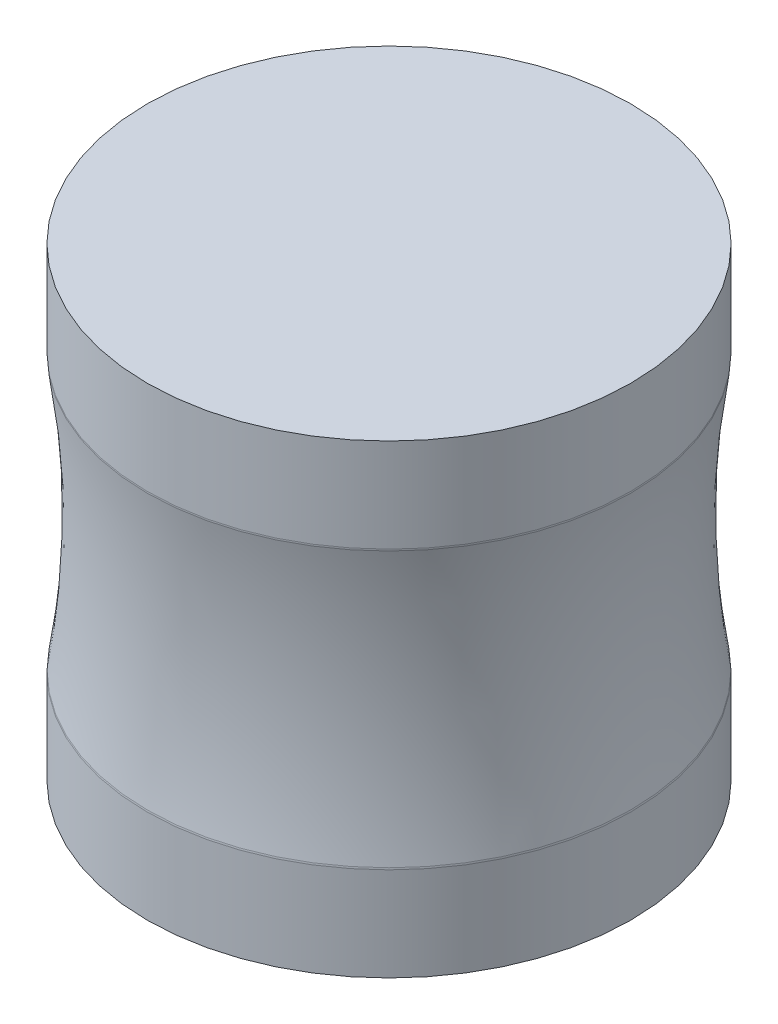
SolidWorks part; units mm, degrees
ref_plane "Ebene vorne" through (0, 0, 0) normal (0, 0, 1) x (1, 0, 0)
ref_plane "Ebene oben" through (0, 0, 0) normal (0, 1, 0) x (1, 0, 0)
ref_plane "Ebene rechts" through (0, 0, 0) normal (1, 0, 0) x (0, 0, -1)
sketch "Skizze1" plane through (0, 0, 0) normal (0, 0, 1) x (1, 0, 0)
  line L0 (109.5273, -62.8727) -> (109.5273, -105.2597)
  line L1 (0, 105.2597) -> (109.5273, 105.2597)
  line L2 (0, 105.2597) -> (0, -105.2597)
  line L3 (0, -105.2597) -> (109.5273, -105.2597)
  line L4 (109.5273, 105.2597) -> (109.5273, 62.8727)
  arc A0 (109.4644, 62.0824) -> (109.4644, -62.0824) centre (497.3248, 0) ccw
  arc A1 (109.4644, -62.0824) -> (109.5273, -62.8727) centre (104.5273, -62.8727) cw
  arc A2 (109.4644, 62.0824) -> (109.5273, 62.8727) centre (104.5273, 62.8727) ccw
  point P10 (109.5273, -62.4738)
  dimension "D1" = 5
  dimension "D2" = 5
  dimension "D3" = 210.5193
revolve "Rotation1" add sketch "Skizze1" angle 360 about L2
ref_plane "Ebene1" through (130, 0, 0) normal (1, 0, 0) x (0, 0, -1)
sketch "Skizze2" plane through (130, 0, 0) normal (1, 0, 0) x (0, 0, -1)
  line L0 (9.6186, 33.5529) -> (53.72, 6.0032)
  line L1 (53.72, 6.0032) -> (28.6987, -20.7444)
  line L2 (28.6987, -20.7444) -> (28.6987, 12.6372)
  line L3 (28.6987, 12.6372) -> (9.6186, 33.5529)
